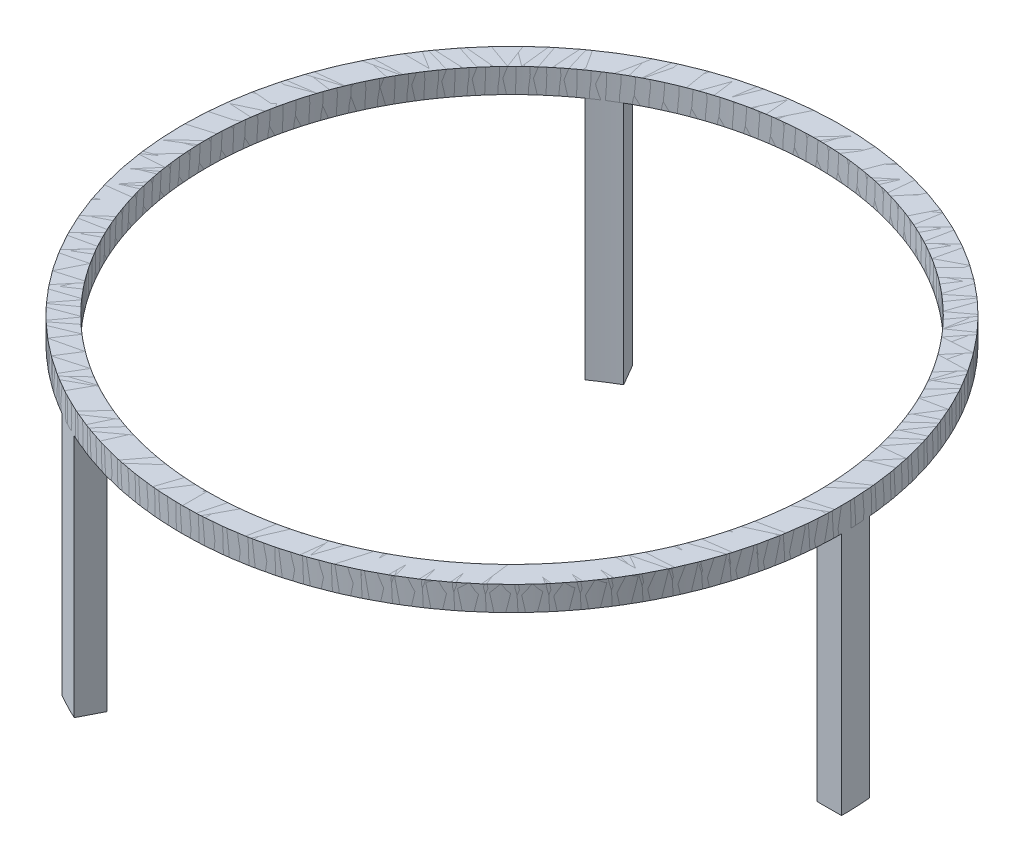
SolidWorks part; units mm, degrees
ref_plane "Front Plane" through (0, 0, 0) normal (0, 0, 1) x (1, 0, 0)
ref_plane "Top Plane" through (0, 0, 0) normal (0, 1, 0) x (1, 0, 0)
ref_plane "Right Plane" through (0, 0, 0) normal (1, 0, 0) x (0, 0, -1)
sketch "Sketch2" plane through (0, 0, 0) normal (0, 1, 0) x (1, 0, 0)
  circle A0 centre (0, 0) radius 125
  circle A1 centre (0, 0) radius 135
extrude "Boss-Extrude1" add sketch "Sketch2" along normal blind 10
sketch "Sketch4" plane through (0, 0, 0) normal (0, -1, 0) x (1, 0, 0)
  line L0 (125, 0) -> (135, -0.0203)
  line L1 (124.4785, -11.4063) -> (134.4742, -11.9037)
  arc A0 (125, 0) -> (124.4785, -11.4063) centre (0, 0) cw
  circle A1 centre (0, 0) radius 125 construction
  arc A2 (135, -0.0203) -> (134.4742, -11.9037) centre (0, 0) cw
  circle A3 centre (0, 0) radius 135 construction
extrude "Boss-Extrude2" add sketch "Sketch4" along normal blind 100
pattern_circular "CirPattern1" count 3 over 360 about axis through (0, 0, 0) along (0, 1, 0) of bodies 102
